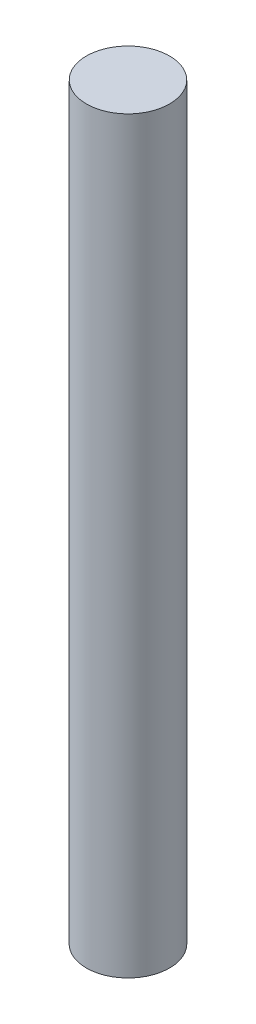
SolidWorks part; units mm, degrees
material "Rubber"
ref_plane "Front Plane" through (0, 0, 0) normal (0, 0, 1) x (1, 0, 0)
ref_plane "Top Plane" through (0, 0, 0) normal (0, 1, 0) x (1, 0, 0)
ref_plane "Right Plane" through (0, 0, 0) normal (1, 0, 0) x (0, 0, -1)
sketch "Sketch1" plane through (0, 0, 0) normal (0, 1, 0) x (1, 0, 0)
  circle A0 centre (0, 0) radius 6.35
  dimension "D1" = 12.7
extrude "Boss-Extrude1" add sketch "Sketch1" along normal mid plane 114.3
